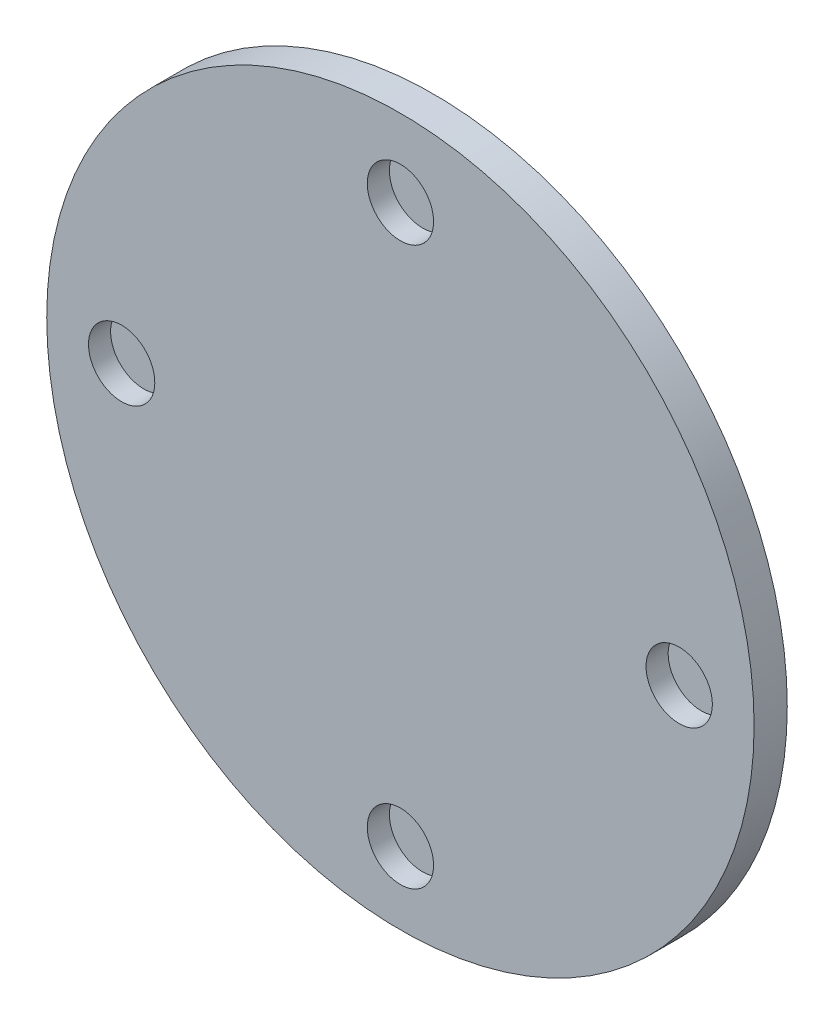
SolidWorks part; units mm, degrees
ref_plane "Piano frontale" through (0, 0, 0) normal (0, 0, 1) x (1, 0, 0)
ref_plane "Piano superiore" through (0, 0, 0) normal (0, 1, 0) x (1, 0, 0)
ref_plane "Piano destro" through (0, 0, 0) normal (1, 0, 0) x (0, 0, -1)
sketch "Schizzo1" plane through (0, 0, 0) normal (0, 0, 1) x (1, 0, 0)
  circle A0 centre (0, 0) radius 16
  dimension "D1" = 32
extrude "Estrusione-Estrusione1" add sketch "Schizzo1" against normal blind 1.5 contours A0
sketch "Schizzo7" plane through (0, 0, 0) normal (0, 0, 1) x (1, 0, 0)
  circle A0 centre (0, 12.5) radius 1.5
  dimension "D1" = 3
  dimension "D2" = 12.5
extrude "Taglio-Estrusione1" cut sketch "Schizzo7" against normal blind 1
pattern_circular "RipetizioneCircolare1" count 4 over 360 about axis through (0, -0.1108, 0) along (0, 0, 1) of "Taglio-Estrusione1"
